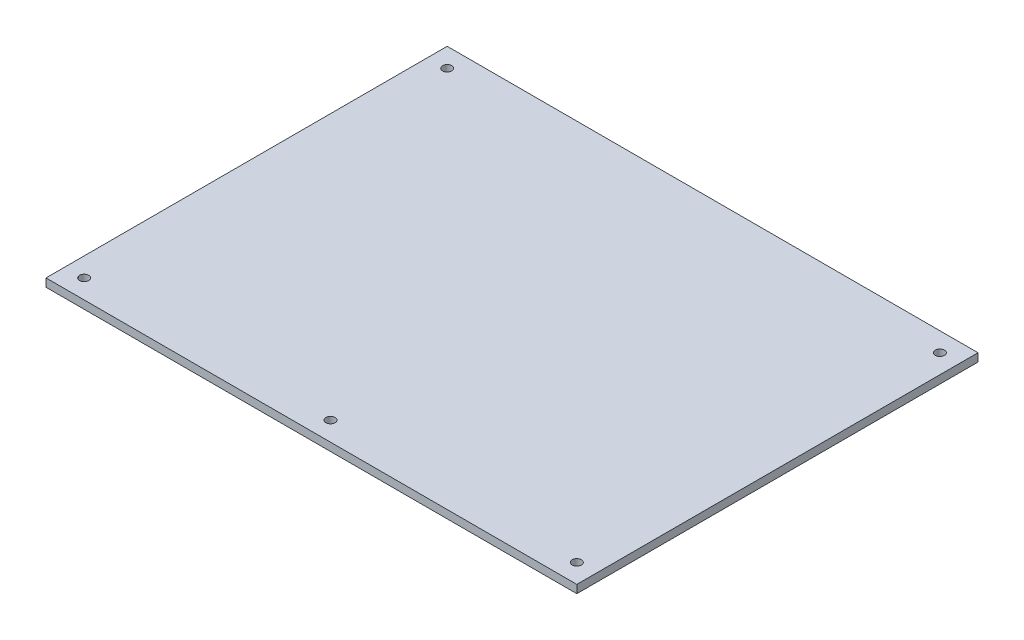
SolidWorks part; units mm, degrees
ref_plane "Front Plane" through (0, 0, 0) normal (0, 0, 1) x (1, 0, 0)
ref_plane "Top Plane" through (0, 0, 0) normal (0, 1, 0) x (1, 0, 0)
ref_plane "Right Plane" through (0, 0, 0) normal (1, 0, 0) x (0, 0, -1)
sketch "Sketch1" plane through (0, 0, 0) normal (0, 1, 0) x (1, 0, 0)
  line L1 (-246.1199, -301.6249) -> (169.9601, -301.6249)
  line L2 (-246.1199, -301.6249) -> (-246.1199, 12.8551)
  line L3 (-246.1199, 12.8551) -> (169.9601, 12.8551)
  line L4 (169.9601, -301.6249) -> (169.9601, 12.8551)
  line L5 (-246.1199, -301.6249) -> (-246.1199, 12.8551) construction
extrude "Boss-Extrude1" add sketch "Sketch1" along normal blind 6.35
sketch "Sketch2" plane through (0, 6.35, 0) normal (0, 1, 0) x (1, 0, 0)
  circle A0 centre (-231.1699, -2.0949) radius 3.6
  circle A1 centre (155.0101, -2.0949) radius 3.6
  circle A2 centre (155.0101, -286.6749) radius 3.6
  circle A3 centre (-38.0799, -286.6749) radius 3.6
  circle A4 centre (-231.1699, -286.6749) radius 3.6
  arc A5 (-227.9436, -3.692) -> (-227.9436, -0.4977) centre (-231.1699, -2.0949) ccw construction
  point P15 (-227.5699, -2.0949)
  point P16 (-227.5699, -2.0949)
extrude "Cut-Extrude1" cut sketch "Sketch2" against normal through all
